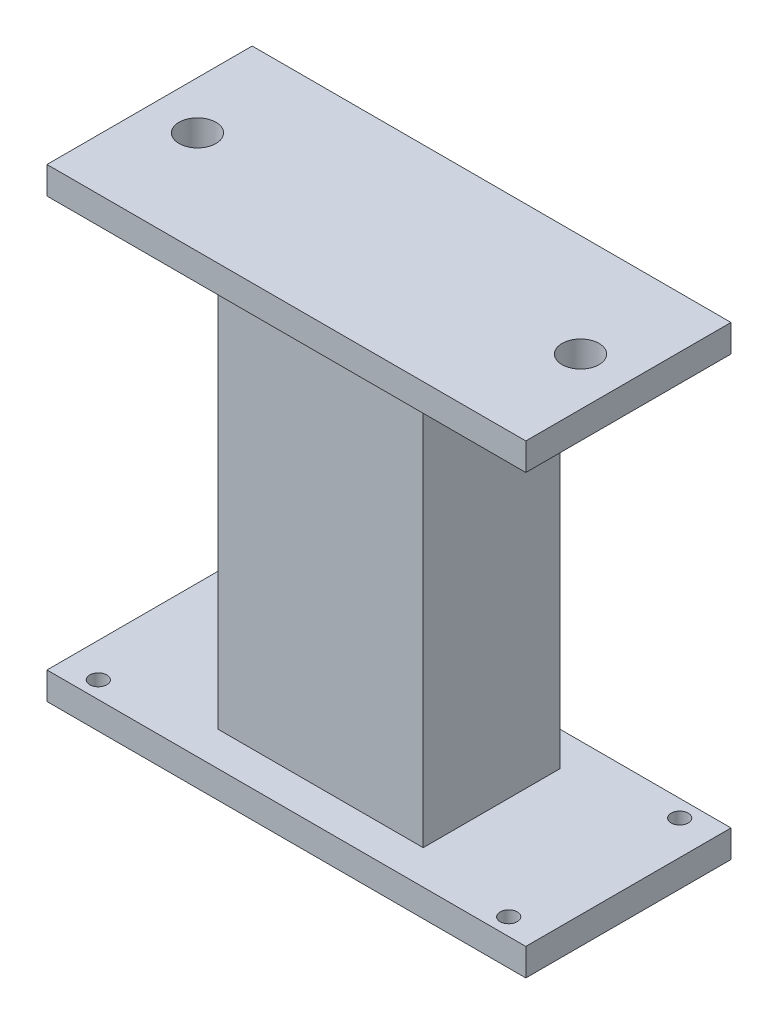
SolidWorks part; units mm, degrees
ref_plane "Front Plane" through (0, 0, 0) normal (0, 0, 1) x (1, 0, 0)
ref_plane "Top Plane" through (0, 0, 0) normal (0, 1, 0) x (1, 0, 0)
ref_plane "Right Plane" through (0, 0, 0) normal (1, 0, 0) x (0, 0, -1)
sketch "Sketch2" plane through (0, 0, 0) normal (0, 1, 0) x (1, 0, 0)
  line L0 (-44.1575, 0) -> (50.7314, 0) construction
  line L1 (-35, 15) -> (35, 15)
  line L2 (-35, 15) -> (-35, -15)
  line L3 (-35, -15) -> (35, -15)
  line L4 (35, 15) -> (35, -15)
  line L5 (-35, 15) -> (35, -15) construction
  line L6 (-35, -15) -> (35, 15) construction
  line L7 (0, 22.1555) -> (0, -22.17) construction
  circle A1 centre (-30, -12.5) radius 1.25
  circle A2 centre (-30, 12.5) radius 1.25
  circle A3 centre (30, -12.5) radius 1.25
  circle A4 centre (30, 12.5) radius 1.25
  point P0 (0, 0)
  dimension "D5" = 2.5
  dimension "D1" = 70
  dimension "D2" = 30
  dimension "D3" = 2.5
  dimension "D4" = 5
extrude "Boss-Extrude1" add sketch "Sketch2" along normal blind 4
sketch "Sketch4" plane through (0, 4, 0) normal (0, 1, 0) x (1, 0, 0)
  line L1 (-15, 10) -> (15, 10)
  line L2 (-15, 10) -> (-15, -10)
  line L3 (-15, -10) -> (15, -10)
  line L4 (15, 10) -> (15, -10)
  line L5 (-15, 10) -> (15, -10) construction
  line L6 (-15, -10) -> (15, 10) construction
  point P0 (0, 0)
  dimension "D1" = 30
  dimension "D2" = 20
extrude "Boss-Extrude2" add sketch "Sketch4" along normal blind 60.0001
ref_plane "Plane1" through (0, 13.65, 0) normal (0, 1, 0) x (1, 0, 0)
sketch "Sketch5" plane through (0, 64.0001, 0) normal (0, 1, 0) x (1, 0, 0)
  line L0 (0, 18.245) -> (0, -25.8243) construction
  line L1 (-35, 15) -> (35, 15)
  line L2 (-35, 15) -> (-35, -15)
  line L3 (-35, -15) -> (35, -15)
  line L4 (35, 15) -> (35, -15)
  line L5 (-35, 15) -> (35, -15) construction
  line L6 (-35, -15) -> (35, 15) construction
  circle A0 centre (-28, 0) radius 2.7
  circle A1 centre (28, 0) radius 2.7
  point P0 (0, 0)
  dimension "D1" = 5.4
  dimension "D2" = 28
  dimension "D3" = 7
extrude "Boss-Extrude3" add sketch "Sketch5" along normal blind 4
equation "\"base_width\"= 7cm"
equation "\"base_length\"= 3cm"
equation "\"hole_cdx\"= 0.5cm"
equation "\"hole_cdy\"= 0.25cm"
equation "\"hole_diam\"= 0.25cm"
equation "\"D1@Sketch2\"=\"base_width\""
equation "\"D2@Sketch2\"=\"base_length\""
equation "\"D3@Sketch2\"=\"hole_cdy\""
equation "\"D4@Sketch2\"=\"hole_cdx\""
equation "\"D5@Sketch2\"=\"hole_diam\""
equation "\"mount_height\"= 0.4cm"
equation "\"D1@Boss-Extrude1\"=\"mount_height\""
equation "\"neck_width\"= 3cm"
equation "\"neck_length\"= 2cm"
equation "\"neck_dy\"= 0.5cm"
equation "\"D1@Sketch4\"=\"neck_width\""
equation "\"D2@Sketch4\"=\"neck_length\""
equation "\"neck_height\"= 1.93cm"
equation "\"D1@Boss-Extrude2\"=\"neck_height\"+4.47001011cm-0.4cm"
equation "\"D2@Sketch5\"=\"ball_hole_pos\""
equation "\"ball_mount_diam\"= 5.4mm"
equation "\"ball_hole_pos\"= 28mm"
equation "\"D1@Sketch5\"=\"ball_mount_diam\""
equation "\"D1@Boss-Extrude3\"=\"mount_height\""
